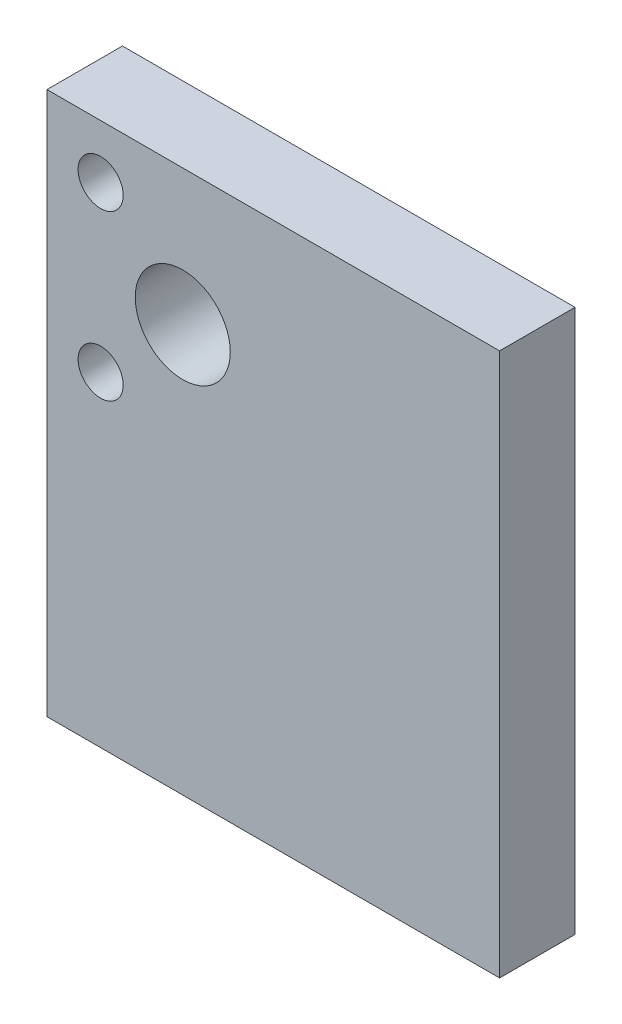
SolidWorks part; units mm, degrees
material "6061-T6 (SS)"
ref_plane "Front Plane" through (0, 0, 0) normal (0, 0, 1) x (1, 0, 0)
ref_plane "Top Plane" through (0, 0, 0) normal (0, 1, 0) x (1, 0, 0)
ref_plane "Right Plane" through (0, 0, 0) normal (1, 0, 0) x (0, 0, -1)
sketch "Sketch1" plane through (0, 0, 0) normal (0, 0, 1) x (1, 0, 0)
  line L1 (0, 0) -> (38.1, 0)
  line L2 (0, 0) -> (0, 45.72)
  line L3 (0, 45.72) -> (38.1, 45.72)
  line L4 (38.1, 0) -> (38.1, 45.72)
  dimension "D1" = 45.72
  dimension "D2" = 38.1
extrude "Boss-Extrude1" add sketch "Sketch1" along normal blind 6.35
sketch "Sketch2" plane through (0, 0, 6.35) normal (0, 0, 1) x (1, 0, 0)
  line L0 (38.1, 45.72) -> (0, 45.72) construction
  line L1 (0, 45.72) -> (0, 0) construction
  circle A0 centre (11.43, 34.29) radius 4
  dimension "D1" = 8
  dimension "D2" = 11.43
  dimension "D3" = 11.43
extrude "Cut-Extrude1" cut sketch "Sketch2" against normal through all both and the other way through all
hole_wizard "#6 Clearance Hole2" positions "Sketch5" profile "Sketch6" hole size "#6" standard "ANSI Inch" end condition up to next
sketch "Sketch5" plane through (0, 0, 6.35) normal (0, 0, 1) x (1, 0, 0)
  point P0 (4.5152, 41.2048)
  point P3 (4.5152, 27.3752)
sketch "Sketch6" plane through (4.5152, 41.2048, 6.35) normal (1, 0, 0) x (0, -1, 0)
  line L0 (0, 0) -> (0, 6.35)
  line L1 (0, 6.35) -> (1.8986, 6.35)
  line L2 (1.8986, 6.35) -> (1.8986, 0)
  line L5 (1.8986, 0) -> (0, 0)
  line L11 (0, -6.35) -> (0, 107.95) construction
  dimension "Thru Hole Dia." = 3.7973
  dimension "Thru Hole Depth" = 6.35
